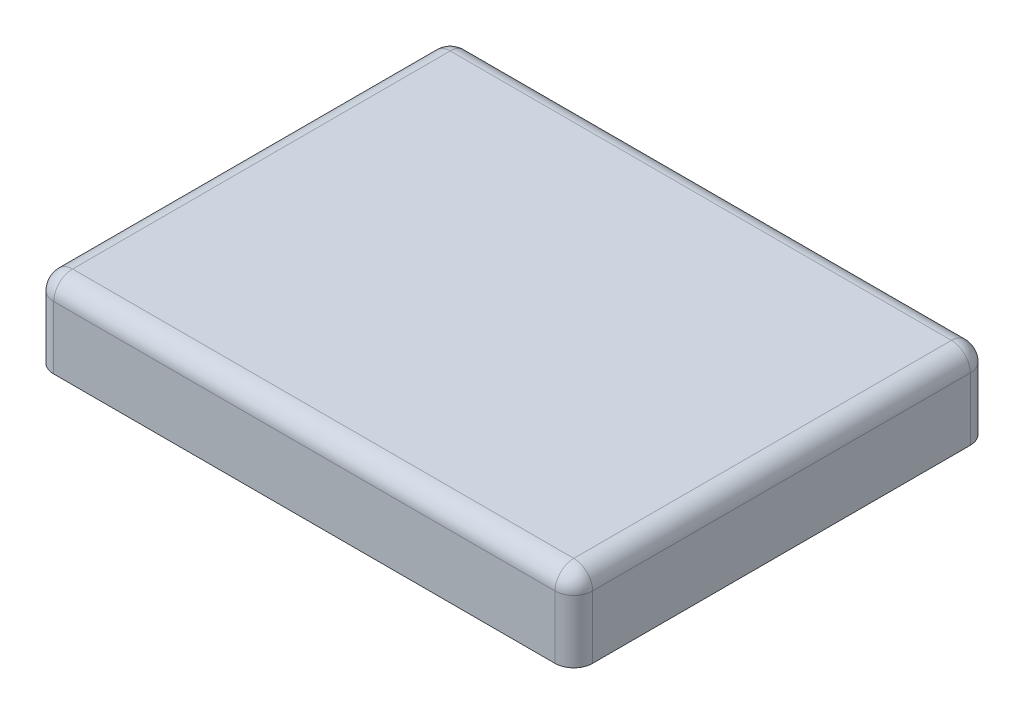
SolidWorks part; units mm, degrees
ref_plane "Front Plane" through (0, 0, 0) normal (0, 0, 1) x (1, 0, 0)
ref_plane "Top Plane" through (0, 0, 0) normal (0, 1, 0) x (1, 0, 0)
ref_plane "Right Plane" through (0, 0, 0) normal (1, 0, 0) x (0, 0, -1)
sketch "Sketch1" plane through (0, 0, 0) normal (0, 1, 0) x (1, 0, 0)
  line L1 (0, 0) -> (436.372, 0)
  line L2 (0, 0) -> (0, 336.296)
  line L3 (0, 336.296) -> (436.372, 336.296)
  line L4 (436.372, 0) -> (436.372, 336.296)
  dimension "D1" = 436.372
  dimension "D2" = 336.296
extrude "Boss-Extrude1" add sketch "Sketch1" along normal blind 66.04
fillet "Fillet1" radius 15.24 8 edges at (0, 33.02, -336.296) (218.186, 66.04, -336.296) (436.372, 33.02, -336.296) (436.372, 66.04, -168.148) (436.372, 33.02, 0) (0, 33.02, 0) (0, 66.04, -168.148) (218.186, 66.04, 0)
